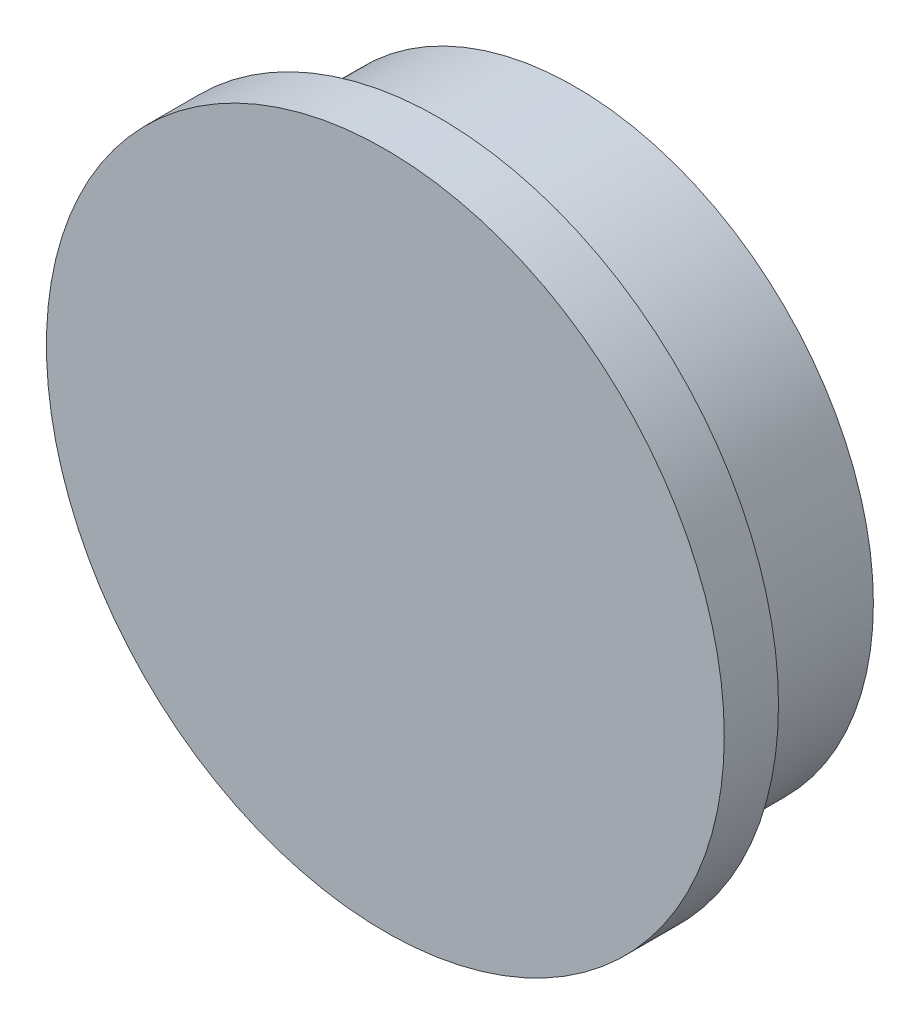
SolidWorks part; units mm, degrees
ref_plane "Front Plane" through (0, 0, 0) normal (0, 0, 1) x (1, 0, 0)
ref_plane "Top Plane" through (0, 0, 0) normal (0, 1, 0) x (1, 0, 0)
ref_plane "Right Plane" through (0, 0, 0) normal (1, 0, 0) x (0, 0, -1)
sketch "Sketch1" plane through (0, 0, 0) normal (0, 0, 1) x (1, 0, 0)
  circle A1 centre (35.4584, -19.2888) radius 5.588
  dimension "D2" = 11.176
extrude "Boss-Extrude1" add sketch "Sketch1" against normal blind 2.54
sketch "Sketch2" plane through (0, 0, 0) normal (0, 0, 1) x (1, 0, 0)
  circle A0 centre (35.4584, -19.2888) radius 6.35
  dimension "D1" = 12.7
extrude "Boss-Extrude2" add sketch "Sketch2" along normal blind 1.016
